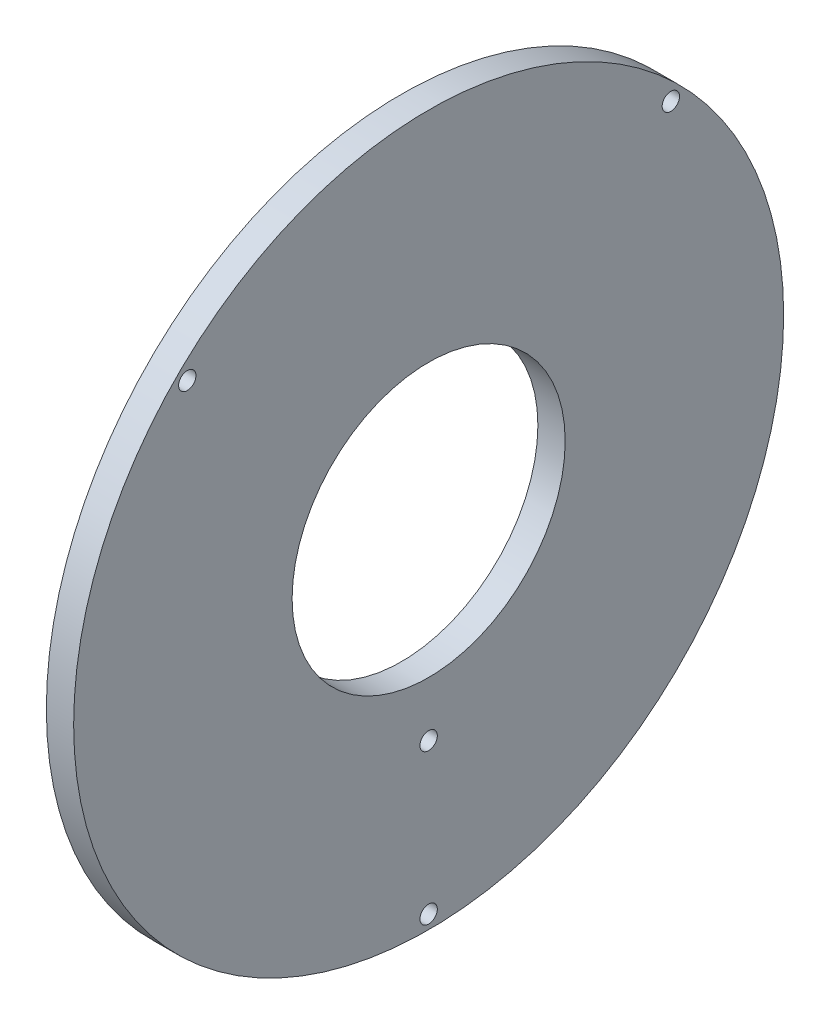
SolidWorks part; units mm, degrees
material "Copper"
ref_plane "Front Plane" through (0, 0, 0) normal (0, 0, 1) x (1, 0, 0)
ref_plane "Top Plane" through (0, 0, 0) normal (0, 1, 0) x (1, 0, 0)
ref_plane "Right Plane" through (0, 0, 0) normal (1, 0, 0) x (0, 0, -1)
sketch "Sketch1" plane through (0, 0, 0) normal (1, 0, 0) x (0, 0, -1)
  circle A0 centre (0, 0) radius 260
extrude "Boss-Extrude1" add sketch "Sketch1" along normal blind 20
ref_plane "Plane1" through (20, 0, 0) normal (1, 0, 0) x (0, 0, -1)
sketch "Sketch2" plane through (20, 0, 0) normal (1, 0, 0) x (0, 0, -1)
  line L0 (183.8478, 183.8478) -> (169.7056, 169.7056)
  line L1 (-183.8478, 183.8478) -> (-169.7056, 169.7056)
  line L2 (0, 0) -> (0, -100)
  line L3 (169.7056, -169.7056) -> (183.8478, -183.8478)
  line L4 (-169.7056, -169.7056) -> (-183.8478, -183.8478)
  line L5 (0, -240) -> (0, -260)
  line L6 (0, 0) -> (0, -140)
  circle A0 centre (0, 0) radius 260
  arc A1 (-169.7056, -169.7056) -> (169.7056, -169.7056) centre (0, 0) ccw
  circle A2 centre (0, 0) radius 100
  point P11 (-176.7767, 176.7767)
  point P12 (0, -250)
  point P13 (177.3676, 176.7767)
  point P15 (176.7767, -176.7767)
  point P16 (-176.7767, -176.7767)
  point P17 (0, -240)
extrude "Cut-Extrude1" cut sketch "Sketch2" against normal blind 20 contours A2
hole_wizard "1/2-13 Tapped Hole1" positions "3DSketch2" profile "Sketch4" tap size "1/2-13" standard "ANSI Inch"
sketch3d "3DSketch2"
  point P0 (20, 176.7767, -177.3676)
  point P3 (20, 176.7767, 176.7767)
  point P15 (20, -250, 0)
  point P18 (20, -140, 0)
sketch "Sketch4" plane through (20, 176.7767, -177.3676) normal (0, 1, 0) x (0, 0, -1)
  line L0 (0, 0) -> (0, 73.6195)
  line L1 (0, 73.6195) -> (5.3581, 70.4)
  line L2 (5.3581, 70.4) -> (5.3581, 64.5)
  line L3 (5.3581, 64.5) -> (6.35, 64.5)
  line L4 (6.35, 64.5) -> (6.35, 0)
  line L5 (6.35, 0) -> (0, 0)
  line L10 (0, 73.6195) -> (-5.3581, 70.4) construction
  line L11 (0, -6.35) -> (0, 107.95) construction
  dimension "Tap Drill Dia." = 10.7163
  dimension "Tap Drill Depth" = 70.4
  dimension "Thread Major Dia." = 12.7
  dimension "Thread Depth" = 64.5
  dimension "Drill Angle" = 118
